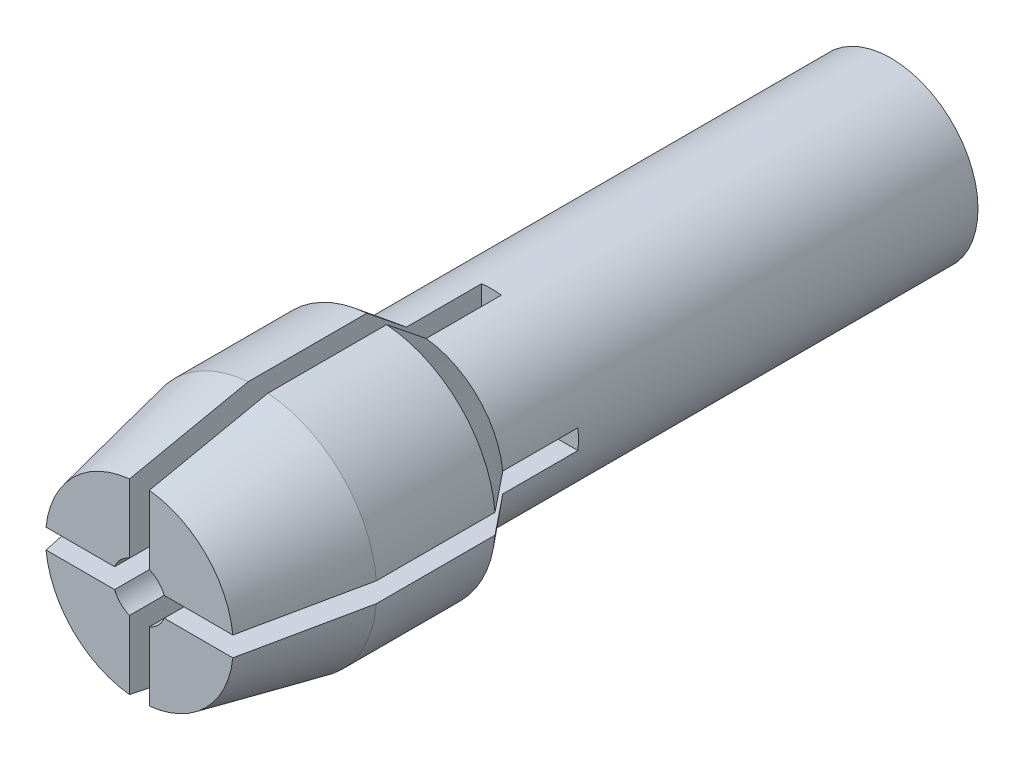
SolidWorks part; units mm, degrees
ref_plane "Front Plane" through (0, 0, 0) normal (0, 0, 1) x (1, 0, 0)
ref_plane "Top Plane" through (0, 0, 0) normal (0, 1, 0) x (1, 0, 0)
ref_plane "Right Plane" through (0, 0, 0) normal (1, 0, 0) x (0, 0, -1)
sketch "Sketch1" plane through (0, 0, 0) normal (0, 0, 1) x (1, 0, 0)
  circle A0 centre (0, 0) radius 2.2
  circle A1 centre (0, 0) radius 1.25
  dimension "D1" = 4.4
  dimension "D2" = 2.5
extrude "Boss-Extrude1" add sketch "Sketch1" along normal blind 12
sketch "Sketch2" plane through (0, 0, 12) normal (0, 0, 1) x (1, 0, 0)
  circle A0 centre (0, 0) radius 3
  circle A1 centre (0, 0) radius 0.675
  dimension "D1" = 6
  dimension "D2" = 1.35
extrude "Boss-Extrude2" add sketch "Sketch2" along normal blind 7
sketch "Sketch3" plane through (0, 0, 0) normal (0, 1, 0) x (1, 0, 0)
  line L0 (2.2, -12) -> (3, -13)
  line L1 (2.2, -12) -> (2.2, 0) construction
  line L2 (3, -12) -> (-3, -12) construction
  line L3 (3, -19) -> (3, -12) construction
  line L4 (2.2, -12) -> (3.4678, -11.1521)
  line L5 (3.4678, -11.1521) -> (4.2763, -12.3611)
  line L6 (4.2763, -12.3611) -> (3, -13)
  line L7 (0, -19) -> (2.375, -19) construction
  line L8 (-3, -19) -> (3, -19) construction
  line L9 (2.375, -19) -> (3, -16)
  line L10 (3, -16) -> (5.7518, -17.1718)
  line L11 (5.7518, -17.1718) -> (4.2549, -20.9396)
  line L12 (4.2549, -20.9396) -> (2.375, -19)
  dimension "D1" = 1
  dimension "D2" = 2.375
  dimension "D3" = 3
sketch3d "3DSketch1"
  line L0 (0, 0, 0) -> (0, 0, 19) construction
revolve "Cut-Revolve1" cut sketch "Sketch3" angle 360 about L0
sketch "Sketch4" plane through (0, 0, 19) normal (0, 0, 1) x (1, 0, 0)
  line L0 (0, 0) -> (0, 3.3408) construction
  line L1 (0, 3.3408) -> (-0.25, 3.3408)
  line L2 (-0.25, 3.3408) -> (-0.25, 0.4648)
  line L3 (-0.25, 0.4648) -> (0.25, 0.4648)
  line L4 (0.25, 0.4648) -> (0.25, 3.3408)
  line L5 (0.25, 3.3408) -> (0, 3.3408)
  line L6 (3.3408, 0) -> (3.3408, 0.25)
  line L7 (3.3408, 0.25) -> (0.4648, 0.25)
  line L8 (0.4648, 0.25) -> (0.4648, -0.25)
  line L9 (0.4648, -0.25) -> (3.3408, -0.25)
  line L10 (3.3408, -0.25) -> (3.3408, 0)
  line L11 (0, 0) -> (3.3408, 0) construction
  line L12 (0, -3.3408) -> (0.25, -3.3408)
  line L13 (0.25, -3.3408) -> (0.25, -0.4648)
  line L14 (0.25, -0.4648) -> (-0.25, -0.4648)
  line L15 (-0.25, -0.4648) -> (-0.25, -3.3408)
  line L16 (-0.25, -3.3408) -> (0, -3.3408)
  line L17 (0, 0) -> (0, -3.3408) construction
  line L18 (-3.3408, 0) -> (-3.3408, -0.25)
  line L19 (-3.3408, -0.25) -> (-0.4648, -0.25)
  line L20 (-0.4648, -0.25) -> (-0.4648, 0.25)
  line L21 (-0.4648, 0.25) -> (-3.3408, 0.25)
  line L22 (-3.3408, 0.25) -> (-3.3408, 0)
  line L23 (0, 0) -> (-3.3408, 0) construction
  point P25 (0, 0)
  dimension "D1" = 0.25
  dimension "D2" = 0.25
  dimension "D3" = 4
extrude "Cut-Extrude1" cut sketch "Sketch4" against normal blind 8.9
equation "\"D2@Sketch3\"=4.75/2"
